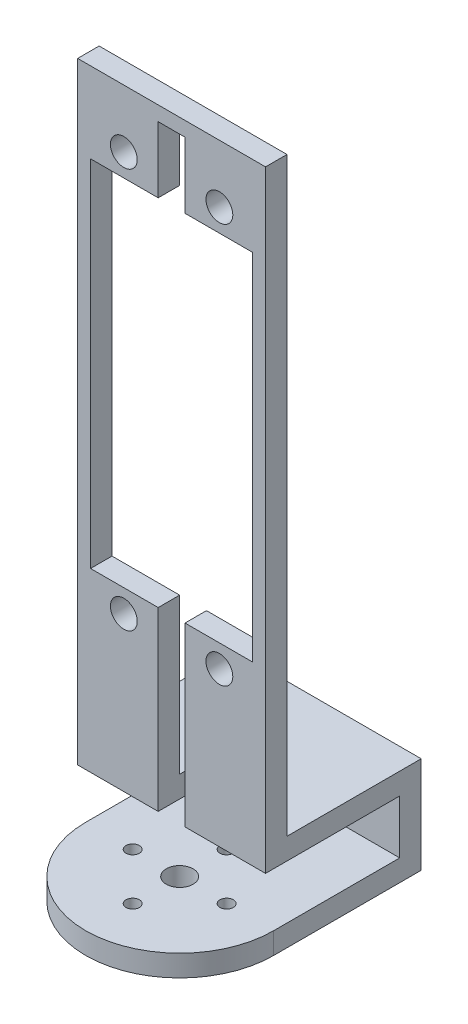
SolidWorks part; units mm, degrees
ref_plane "Front Plane" through (0, 0, 0) normal (0, 0, 1) x (1, 0, 0)
ref_plane "Top Plane" through (0, 0, 0) normal (0, 1, 0) x (1, 0, 0)
ref_plane "Right Plane" through (0, 0, 0) normal (1, 0, 0) x (0, 0, -1)
sketch "Sketch3" plane through (0, 0, 0) normal (0, 1, 0) x (1, 0, 0)
  line L0 (-17.5, 0) -> (-17.5, 27.5)
  line L1 (-17.5, 27.5) -> (17.5, 27.5)
  line L2 (17.5, 27.5) -> (17.5, 0)
  arc A0 (-17.5, 0) -> (17.5, 0) centre (0, 0) ccw
  dimension "D1" = 27.5
extrude "Boss-Extrude2" add sketch "Sketch3" along normal blind 4
sketch "Sketch4" plane through (0, 4, 0) normal (0, 1, 0) x (1, 0, 0)
  line L0 (17.5, 0) -> (17.5, 27.5) construction
  line L1 (-17.5, 27.5) -> (17.5, 27.5)
  line L2 (-17.5, 27.5) -> (-17.5, 23.5)
  line L3 (-17.5, 23.5) -> (17.5, 23.5)
  line L4 (17.5, 27.5) -> (17.5, 23.5)
extrude "Boss-Extrude3" add sketch "Sketch4" along normal blind 10
sketch "Sketch6" plane through (-17.5, 0, 0) normal (-1, 0, 0) x (0, 0, 1)
  line L0 (-27.5, 14) -> (-27.5, 18)
  line L1 (-27.5, 18) -> (-2.5, 18)
  line L2 (-2.5, 18) -> (-2.5, 128)
  line L3 (-2.5, 128) -> (1.5, 128)
  line L4 (1.5, 128) -> (1.5, 14)
  line L5 (1.5, 14) -> (-27.5, 14)
extrude "Boss-Extrude4" add sketch "Sketch6" against normal blind 35
sketch "Sketch9" plane through (0, 0, 1.5) normal (0, 0, 1) x (1, 0, 0)
  line L0 (-17.5, 128) -> (-17.5, 113) construction
  line L1 (-17.5, 14) -> (-17.5, 128) construction
  line L2 (-17.5, 113) -> (-15.1, 113) construction
  line L3 (-15.1, 113) -> (-8.9, 113) construction
  line L4 (-15.1, 113) -> (-2.5, 113)
  line L5 (-15.1, 113) -> (-15.1, 46.9)
  line L6 (-15.1, 46.9) -> (-2.5, 46.9)
  line L7 (15.1, 113) -> (15.1, 46.9)
  line L8 (-8.9, 113) -> (-8.9, 117.2) construction
  line L10 (2.5, 46.9) -> (2.5, 10)
  line L11 (0, 125.2879) -> (2.5, 125.2879)
  line L12 (2.5, 125.2879) -> (2.5, 113)
  line L13 (2.5, 10) -> (-2.5, 10)
  line L14 (-2.5, 113) -> (-2.5, 125.2879)
  line L15 (-2.5, 125.2879) -> (0, 125.2879)
  line L16 (2.5, 113) -> (15.1, 113)
  line L17 (-2.5, 10) -> (-2.5, 46.9)
  line L18 (2.5, 46.9) -> (15.1, 46.9)
  circle A0 centre (-8.9, 117.2) radius 2.5
  circle A1 centre (8.9, 117.2) radius 2.5
  circle A2 centre (-8.9, 42.7) radius 2.5
  circle A3 centre (8.9, 42.7) radius 2.5
extrude "Cut-Extrude1" cut sketch "Sketch9" against normal blind 6
sketch "Sketch10" plane through (0, 0, 0) normal (0, -1, 0) x (1, 0, 0)
  line L0 (-17.5, 0) -> (0, 0) construction
  line L1 (0, 0) -> (17.5, 0) construction
  line L2 (0, 17.5) -> (0, 0) construction
  line L3 (0, 0) -> (0, -17.5) construction
  arc A0 (17.5, 0) -> (-17.5, 0) centre (0, 0) ccw construction
  circle A1 centre (-8.75, 0) radius 1.25
  circle A2 centre (8.75, 0) radius 1.25
  circle A3 centre (0, 8.75) radius 1.25
  circle A4 centre (0, -8.75) radius 1.25
extrude "Cut-Extrude2" cut sketch "Sketch10" against normal blind 6
sketch "Sketch11" plane through (0, 0, 0) normal (0, -1, 0) x (1, 0, 0)
  circle A0 centre (0, 0) radius 2.5
extrude "Cut-Extrude3" cut sketch "Sketch11" against normal blind 4
